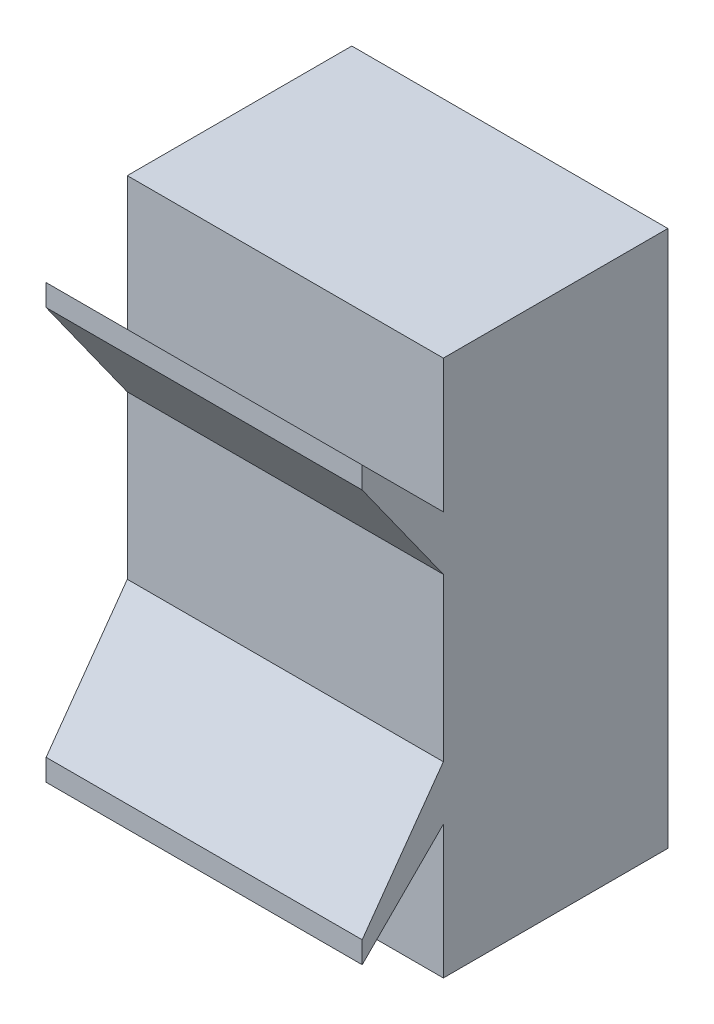
SolidWorks part; units mm, degrees
material "PET"
ref_plane "Front Plane" through (0, 0, 0) normal (0, 0, 1) x (1, 0, 0)
ref_plane "Top Plane" through (0, 0, 0) normal (0, 1, 0) x (1, 0, 0)
ref_plane "Right Plane" through (0, 0, 0) normal (1, 0, 0) x (0, 0, -1)
sketch "Body Base Sketch" plane through (0, 0, 0) normal (0, 0, 1) x (1, 0, 0)
  line L0 (8.7923, 21.2582) -> (14.8348, 21.2582) construction
  line L1 (8.7923, 31.3818) -> (8.7923, 21.2582) construction
  line L2 (14.8348, 21.2582) -> (14.8348, 31.3818) construction
  line L3 (14.8348, 31.3818) -> (8.7923, 31.3818) construction
  line L4 (8.7923, 21.2582) -> (14.8348, 21.2582) construction
  line L5 (8.7923, 31.3818) -> (8.7923, 21.2582) construction
  line L6 (14.8348, 21.2582) -> (14.8348, 31.3818) construction
  line L7 (14.8348, 31.3818) -> (8.7923, 31.3818) construction
  line L8 (8.8923, 21.3582) -> (14.7348, 21.3582)
  line L9 (14.7348, 21.3582) -> (14.7348, 31.2818)
  line L10 (14.7348, 31.2818) -> (8.8923, 31.2818)
  line L11 (8.8923, 31.2818) -> (8.8923, 21.3582)
  dimension "D1" = 0.1
extrude "Body Base" add sketch "Body Base Sketch" along normal offset from surface (4.15 mm away) 0.5
sketch "PCB Spring Sketch" plane through (14.7348, 0, 0) normal (1, 0, 0) x (0, 0, -1)
  line L1 (-4.15, 26.32) -> (-1.2718, 26.32) construction
  line L4 (-4.15, 21.3582) -> (-4.15, 31.2818) construction
  line L5 (-4.15, 24.82) -> (-4.15, 23.82)
  line L6 (-4.65, 25.32) -> (-5.65, 25.32) construction
  line L7 (-4.15, 24.82) -> (-5.65, 22.72)
  line L8 (-5.65, 30.945) -> (-5.65, -2.305) construction
  line L9 (-5.65, 22.72) -> (-5.65, 22.32)
  line L10 (-5.65, 22.32) -> (-4.15, 23.82)
  line L11 (-5.65, 29.92) -> (-5.65, 30.32)
  line L12 (-4.15, 27.82) -> (-5.65, 29.92)
  line L13 (-4.15, 27.82) -> (-4.15, 28.82)
  line L14 (-5.65, 30.32) -> (-4.15, 28.82)
  point P4 (-4.15, 26.32)
  point P5 (-4.15, 26.32)
  dimension "D1" = 1
  dimension "D2" = 0.5
  dimension "D3" = 45
  dimension "D4" = 0.4
extrude "PCB Spring" add sketch "PCB Spring Sketch" against normal up to surface (5.8425 mm away) up to face at (8.8923, 26.32, 2.075)
